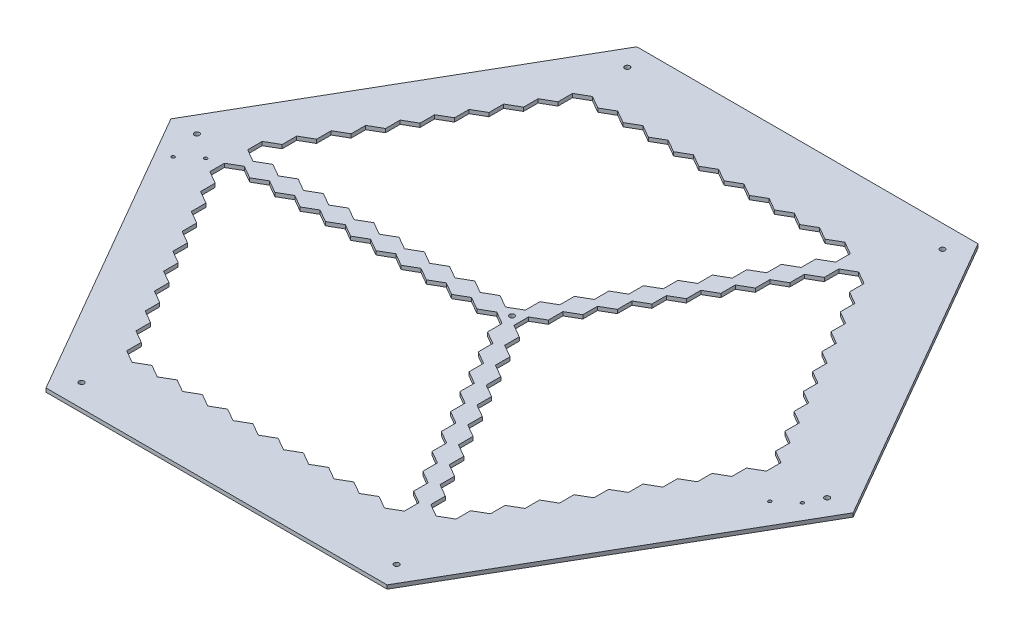
SolidWorks part; units mm, degrees
material "Acrylic (Medium-high impact)"
ref_plane "Front Plane" through (0, 0, 0) normal (0, 0, 1) x (1, 0, 0)
ref_plane "Top Plane" through (0, 0, 0) normal (0, 1, 0) x (1, 0, 0)
ref_plane "Right Plane" through (0, 0, 0) normal (1, 0, 0) x (0, 0, -1)
sketch "Sketch1" plane through (0, 0, 0) normal (0, 1, 0) x (1, 0, 0)
  line L1 (433.0127, 0) -> (216.5064, 375)
  line L2 (216.5064, 375) -> (-216.5064, 375)
  line L3 (-216.5064, 375) -> (-433.0127, 0)
  line L4 (-433.0127, 0) -> (-216.5064, -375)
  line L5 (-216.5064, -375) -> (216.5064, -375)
  line L6 (216.5064, -375) -> (433.0127, 0)
  circle A1 centre (0, 0) radius 375 construction
extrude "Base" add sketch "Sketch1" along normal blind 4.7625
sketch "Border Sketch" plane through (0, 4.7625, 0) normal (0, 1, 0) x (1, 0, 0)
  line L7 (450, 0) -> (225, 389.7114)
  line L8 (225, 389.7114) -> (-225, 389.7114)
  line L9 (-225, 389.7114) -> (-450, 0)
  line L10 (-450, 0) -> (-225, -389.7114)
  line L11 (-225, -389.7114) -> (225, -389.7114)
  line L12 (225, -389.7114) -> (450, 0)
  line L14 (225, 389.7114) -> (0, 0)
  line L15 (0, 0) -> (225, -389.7114)
  line L20 (-450, 0) -> (0, 0)
  line L21 (0, 5.5) -> (-446.8246, 5.5)
  line L22 (0, -5.5) -> (-446.8246, -5.5)
  line L23 (218.6491, 389.7114) -> (-4.7631, 2.75)
  line L24 (4.7631, -2.75) -> (228.1754, 384.2114)
  line L25 (4.7631, 2.75) -> (228.1754, -384.2114)
  line L26 (-4.7631, -2.75) -> (218.6491, -389.7114)
  circle A0 centre (0, 0) radius 450 construction
  circle A1 centre (0, 0) radius 5.5
  dimension "D1" = 5.5
  dimension "D2" = 5.5
  dimension "D3" = 5.5
  dimension "D4" = 5.5
sketch "Sketch3" plane through (0, 4.7625, 0) normal (0, 1, 0) x (1, 0, 0)
  line L8 (-13.8564, -5.5) -> (-29.8779, -14.75)
  line L9 (-29.8779, -14.75) -> (-29.8779, -33.25)
  line L10 (-29.8779, -33.25) -> (-13.8564, -42.5)
  line L11 (-13.8564, -42.5) -> (2.1651, -33.25)
  line L12 (2.1651, -33.25) -> (2.1651, -14.75)
  line L13 (2.1651, -14.75) -> (-13.8564, -5.5)
  line L15 (0, -5.5) -> (-446.8246, -5.5) construction
  line L16 (-4.7631, -2.75) -> (218.6491, -389.7114) construction
  circle A0 centre (-13.8564, -24) radius 18.5 construction
extrude "Bottom Dish Cut" cut sketch "Sketch3" against normal up to next
pattern_linear "Bottom Dish Pattern" count 11 spacing 32.04 along (-1, 0, 0) count 10 spacing 32.04 along (0.5, 0, 0.866) of "Bottom Dish Cut"
sketch "Sketch4" plane through (0, 4.7625, 0) normal (0, 1, 0) x (1, 0, 0)
  line L1 (-13.8564, 42.5) -> (-29.8779, 33.25)
  line L2 (-29.8779, 33.25) -> (-29.8779, 14.75)
  line L3 (-29.8779, 14.75) -> (-13.8564, 5.5)
  line L4 (-13.8564, 5.5) -> (2.1651, 14.75)
  line L5 (2.1651, 14.75) -> (2.1651, 33.25)
  line L6 (2.1651, 33.25) -> (-13.8564, 42.5)
  line L8 (0, 5.5) -> (-446.8246, 5.5) construction
  line L9 (218.6491, 389.7114) -> (-4.7631, 2.75) construction
  circle A0 centre (-13.8564, 24) radius 18.5 construction
extrude "Top Dish Cut" cut sketch "Sketch4" against normal up to next
pattern_linear "Top Dish Pattern" count 11 spacing 32.04 along (-1, 0, 0) count 10 spacing 32.04 along (0.5, 0, -0.866) of "Top Dish Cut"
sketch "Sketch5" plane through (0, 4.7625, 0) normal (0, 1, 0) x (1, 0, 0)
  line L1 (27.7128, 18.5) -> (11.6913, 9.25)
  line L2 (11.6913, 9.25) -> (11.6913, -9.25)
  line L3 (11.6913, -9.25) -> (27.7128, -18.5)
  line L4 (27.7128, -18.5) -> (43.7343, -9.25)
  line L5 (43.7343, -9.25) -> (43.7343, 9.25)
  line L6 (43.7343, 9.25) -> (27.7128, 18.5)
  line L8 (4.7631, 2.75) -> (228.1754, -384.2114) construction
  line L9 (4.7631, -2.75) -> (228.1754, 384.2114) construction
  circle A0 centre (27.7128, 0) radius 18.5 construction
extrude "Right Dish Cut" cut sketch "Sketch5" against normal up to next
pattern_linear "Right Dish Pattern" count 10 spacing 32.04 along (0.5, 0, -0.866) count 10 spacing 32.04 along (0.5, 0, 0.866) of "Right Dish Cut"
hole_wizard "Ø6.5 (6.5) Diameter Hole1" positions "Sketch6" profile "Sketch7" hole size "Ø6.5" standard "ANSI Metric" end condition through all
sketch "Sketch6" plane through (0, 4.7625, 0) normal (0, 1, 0) x (1, 0, 0)
  point P0 (0, 0)
  point P3 (-400, 0)
  point P11 (-200, 346.4102)
  point P12 (200, 346.4102)
  point P13 (400, 0)
  point P14 (200, -346.4102)
  point P15 (-200, -346.4102)
  point P16 (0, 0)
sketch "Sketch7" plane through (0, 4.7625, 0) normal (1, 0, 0) x (0, 0, 1)
  line L0 (0, 0) -> (0, 4.7625)
  line L1 (0, 4.7625) -> (3.25, 4.7625)
  line L2 (3.25, 4.7625) -> (3.25, 0)
  line L3 (3.25, 0) -> (0, 0)
  line L4 (0, -6.35) -> (0, 107.95) construction
  dimension "Thru Hole Dia." = 6.5
  dimension "Thru Hole Depth" = 4.7625
hole_wizard "Ø4.0 (4) Diameter Hole1" positions "Sketch8" profile "Sketch9" hole size "Ø4.0" standard "ANSI Metric" end condition through all
sketch "Sketch8" plane through (0, -9.525, 0) normal (0, -1, 0) x (-1, 0, 0)
  point P0 (-389.7627, -21.2724)
  point P3 (-367.5377, -40.3224)
  point P6 (367.5377, -21.2724)
  point P9 (389.7627, -40.3224)
sketch "Sketch9" plane through (389.7627, -9.525, 21.2724) normal (1, 0, 0) x (0, 0, -1)
  line L0 (0, 0) -> (0, 14.2875)
  line L1 (0, 14.2875) -> (2, 14.2875)
  line L2 (2, 14.2875) -> (2, 0)
  line L3 (2, 0) -> (0, 0)
  line L4 (0, -6.35) -> (0, 107.95) construction
  dimension "Thru Hole Dia." = 4
  dimension "Thru Hole Depth" = 14.2875
